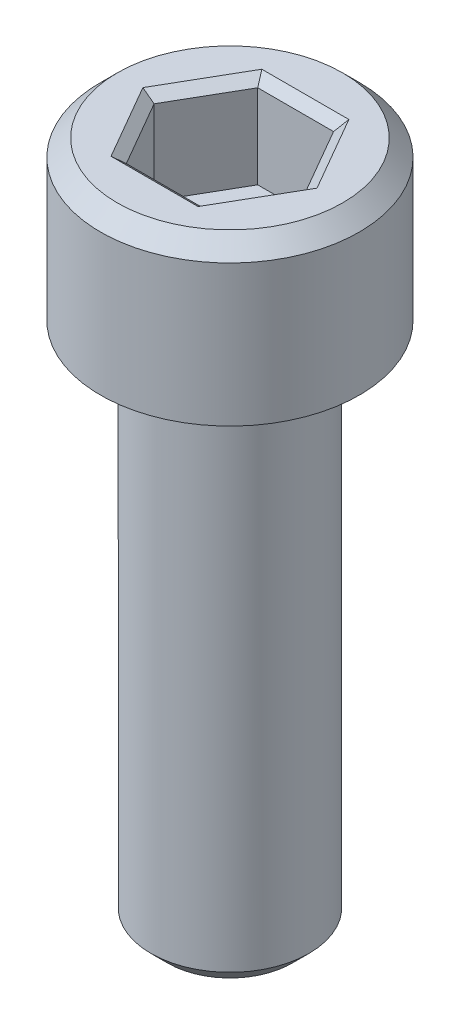
SolidWorks part; units mm, degrees
material "Galvanized Steel"
ref_plane "Front Plane" through (0, 0, 0) normal (0, 0, 1) x (1, 0, 0)
ref_plane "Top Plane" through (0, 0, 0) normal (0, 1, 0) x (1, 0, 0)
ref_plane "Right Plane" through (0, 0, 0) normal (1, 0, 0) x (0, 0, -1)
sketch "Sketch1" plane through (0, 0, 0) normal (0, 0, 1) x (1, 0, 0)
  line L0 (0, 0) -> (0, 14.6665) construction
  line L1 (0, 0) -> (0, 20.6502)
  line L2 (0, 20.6502) -> (-3.9116, 20.6502)
  line L3 (-3.9116, 20.6502) -> (-3.9116, 15.875)
  line L4 (-3.9116, 15.875) -> (-2.3876, 15.875)
  line L5 (-2.3876, 15.875) -> (-2.3876, 0)
  line L6 (-2.3876, 0) -> (0, 0)
  dimension "D1" = 15.875
  dimension "D2" = 4.7752
  dimension "D3" = 4.7752
  dimension "D4" = 7.8232
revolve "Revolve1" add sketch "Sketch1" angle 360 about L0
sketch "Sketch2" plane through (0, 20.6502, 0) normal (0, 1, 0) x (1, 0, 0)
  line L0 (0, 0) -> (2.3879, 0) construction
  line L1 (2.2914, 0) -> (1.1457, 1.9844)
  line L2 (1.1457, 1.9844) -> (-1.1457, 1.9844)
  line L3 (-1.1457, 1.9844) -> (-2.2914, 0)
  line L4 (-2.2914, 0) -> (-1.1457, -1.9844)
  line L5 (-1.1457, -1.9844) -> (1.1457, -1.9844)
  line L6 (1.1457, -1.9844) -> (2.2914, 0)
  circle A0 centre (0, 0) radius 1.9844 construction
  dimension "D1" = 4.5827
extrude "Extrude1" cut sketch "Sketch2" against normal blind 2.794
chamfer "Chamfer1" distance 0.508 angle 45 2 edges at (0, 20.6502, -3.9116) (0, 0, -2.3876)
chamfer "Chamfer2" distance 0.2933 angle 40.893 6 edges at (0, 20.6502, -1.9844) (1.7185, 20.6502, -0.9922) (1.7185, 20.6502, 0.9922) (0, 20.6502, 1.9844) (-1.7185, 20.6502, -0.9922) (-1.7185, 20.6502, 0.9922)
